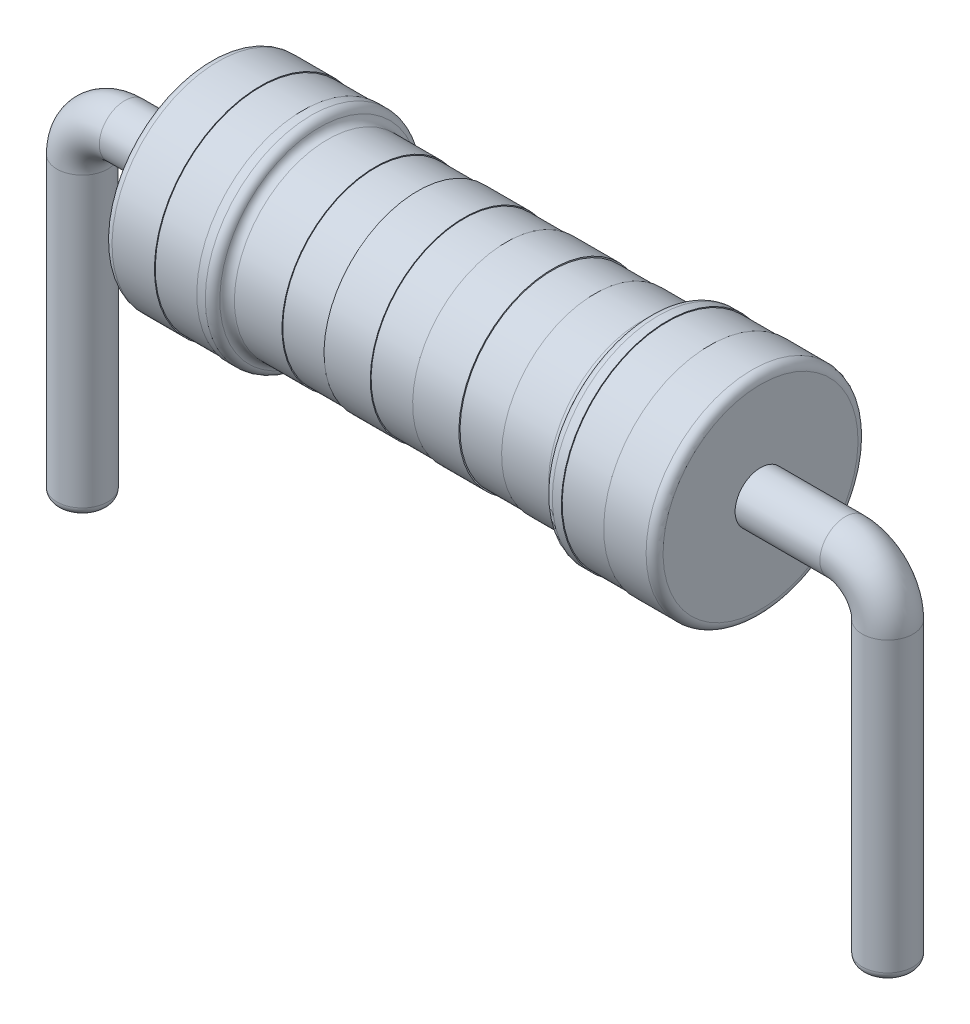
SolidWorks part; units mm, degrees
ref_plane "Front Plane" through (0, 0, 0) normal (0, 0, 1) x (1, 0, 0)
ref_plane "Top Plane" through (0, 0, 0) normal (0, 1, 0) x (1, 0, 0)
ref_plane "Right Plane" through (0, 0, 0) normal (1, 0, 0) x (0, 0, -1)
sketch "Sketch1" plane through (0, 0, 0) normal (0, 0, 1) x (1, 0, 0)
  line L0 (-3.25, 0) -> (3.25, 0)
  line L1 (3.25, 0) -> (3.25, -1.25)
  line L2 (3.25, -1.25) -> (2.65, -1.25)
  line L3 (2.65, -1.25) -> (2.65, -1.24)
  line L4 (2.65, -1.24) -> (2.15, -1.24)
  line L5 (2.15, -1.24) -> (2.15, -1.25)
  line L6 (2.15, -1.25) -> (1.95, -1.25)
  line L7 (1.95, -1.25) -> (1.95, -1.1)
  line L8 (1.95, -1.1) -> (1.2955, -1.1)
  line L9 (1.2955, -1.1) -> (1.2955, -1.09)
  line L10 (1.2955, -1.09) -> (0.7955, -1.09)
  line L11 (0.7955, -1.09) -> (0.7955, -1.1038)
  line L12 (0.7955, -1.1038) -> (0.25, -1.1038)
  line L13 (0.25, -1.1038) -> (0.25, -1.0938)
  line L14 (0.25, -1.0938) -> (-0.25, -1.0938)
  line L16 (-0.25, -1.1038) -> (-0.25, -1.0938)
  line L17 (-0.7955, -1.1038) -> (-0.25, -1.1038)
  line L18 (-0.7955, -1.09) -> (-0.7955, -1.1038)
  line L19 (-1.2955, -1.09) -> (-0.7955, -1.09)
  line L20 (-1.2955, -1.1) -> (-1.2955, -1.09)
  line L21 (-1.95, -1.1) -> (-1.2955, -1.1)
  line L22 (-1.95, -1.25) -> (-1.95, -1.1)
  line L23 (-2.15, -1.25) -> (-1.95, -1.25)
  line L24 (-2.15, -1.24) -> (-2.15, -1.25)
  line L25 (-2.65, -1.24) -> (-2.15, -1.24)
  line L26 (-2.65, -1.25) -> (-2.65, -1.24)
  line L27 (-3.25, -1.25) -> (-2.65, -1.25)
  line L28 (-3.25, 0) -> (-3.25, -1.25)
  point P16 (0, 0)
  dimension "D2" = 1.25
  dimension "D3" = 1.3
  dimension "D4" = 0.5
  dimension "D5" = 0.6
  dimension "D6" = 0.01
  dimension "D7" = 0.01
  dimension "D8" = 0.15
  dimension "D9" = 0.01
  dimension "D10" = 0.0138
  dimension "D11" = 0.01
  dimension "D12" = 0.5
revolve "Revolve3" add sketch "Sketch1" angle 360 about L0
fillet "Fillet3" radius 0.1 2 edges at (-3.25, -1.25, 0) (1.95, -1.1, 0)
fillet "Fillet4" radius 0.1 2 edges at (1.95, -1.25, 0) (-1.95, -1.25, 0)
fillet "Fillet5" radius 0.1 2 edges at (-1.95, -1.1, 0) (3.25, -1.25, 0)
sketch "Sketch2" plane through (3.25, 0, 0) normal (1, 0, 0) x (0, 0, -1)
  circle A0 centre (0, 0) radius 0.3
sketch3d "3DSketch1"
  line L0 (3.25, 0, 0) -> (4.25, 0, 0)
  line L1 (4.75, -0.5, 0) -> (4.75, -4, 0)
  arc A0 (4.75, -0.5, 0) -> (4.25, 0, 0) centre (4.25, -0.5, 0) ccw
  point P6 (4.75, 0, 0)
  point P7 (4.25, -0.5, 0.5)
  dimension "D3" = 0.5
  dimension "D1" = 1.5
  dimension "D2" = 4
sweep "Sweep1" add profiles "Sketch2" path "3DSketch1"
mirror "Mirror1" about plane through (0, 0, 0) normal (1, 0, 0) of "Sweep1"
fillet "Fillet6" radius 0.1 2 edges at (5.05, -4, 0) (-5.05, -4, 0)
